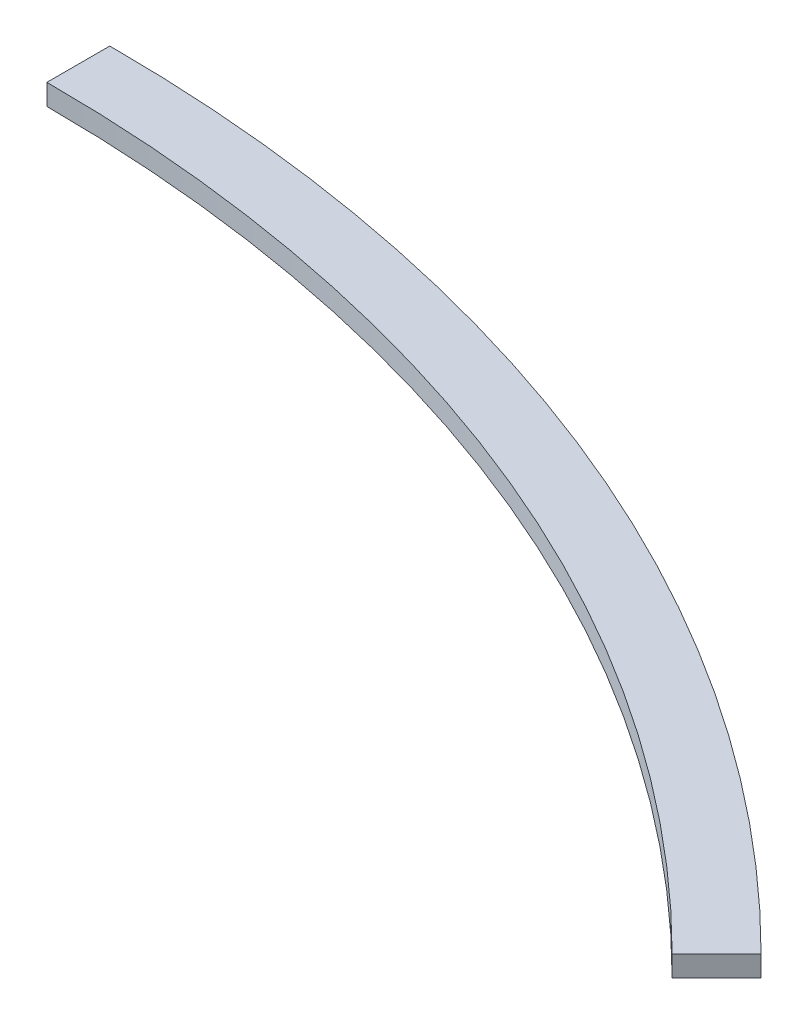
SolidWorks part; units mm, degrees
ref_plane "Front Plane" through (0, 0, 0) normal (0, 0, 1) x (1, 0, 0)
ref_plane "Top Plane" through (0, 0, 0) normal (0, 1, 0) x (1, 0, 0)
ref_plane "Right Plane" through (0, 0, 0) normal (1, 0, 0) x (0, 0, -1)
sketch "Sketch1" plane through (0, 0, 0) normal (0, 1, 0) x (1, 0, 0)
  line L0 (0, 0) -> (0, 720) construction
  line L1 (0, 720) -> (0, 750)
  line L2 (0, 0) -> (530.3301, 530.3301) construction
  line L3 (509.1169, 509.1169) -> (530.3301, 530.3301)
  arc A0 (0, 720) -> (509.1169, 509.1169) centre (0, 0) cw
  arc A1 (0, 750) -> (530.3301, 530.3301) centre (0, 0) cw
  dimension "D1" = 30
  dimension "D2" = 720
  dimension "D3" = 750
  dimension "D4" = 45
extrude "Boss-Extrude1" add sketch "Sketch1" along normal blind 10
